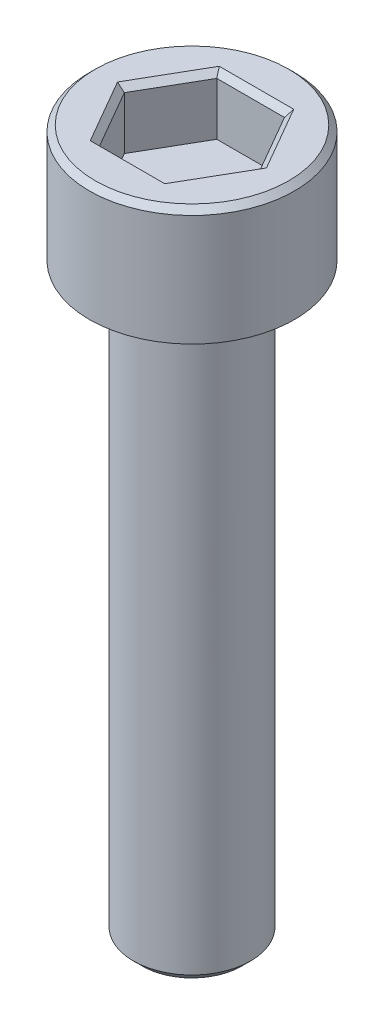
SolidWorks part; units mm, degrees
ref_plane "前视基准面" through (0, 0, 0) normal (0, 0, 1) x (1, 0, 0)
ref_plane "上视基准面" through (0, 0, 0) normal (0, 1, 0) x (1, 0, 0)
ref_plane "右视基准面" through (0, 0, 0) normal (1, 0, 0) x (0, 0, -1)
sketch "草图1" plane through (0, 0, 0) normal (0, 1, 0) x (1, 0, 0)
  circle A0 centre (0, 0) radius 3.5
  dimension "D1" = 7
extrude "凸台-拉伸1" add sketch "草图1" along normal blind 4
sketch "草图2" plane through (0, 0, 0) normal (0, -1, 0) x (1, 0, 0)
  circle A0 centre (0, 0) radius 2
  dimension "D1" = 4
extrude "凸台-拉伸2" add sketch "草图2" along normal blind 20
sketch "草图11" plane through (0, 4, 0) normal (0, 1, 0) x (1, 0, 0)
  line L1 (1.155, 1.9999) -> (-1.1544, 2.0001)
  line L2 (-1.1544, 2.0001) -> (-2.3094, 0.0003)
  line L3 (-2.3094, 0.0003) -> (-1.155, -1.9999)
  line L4 (-1.155, -1.9999) -> (1.1544, -2.0001)
  line L5 (1.1544, -2.0001) -> (2.3094, -0.0003)
  line L6 (2.3094, -0.0003) -> (1.155, 1.9999)
  circle A0 centre (0, 0) radius 2 construction
  dimension "D1" = 4
extrude "切除-拉伸1" cut sketch "草图11" against normal blind 2
chamfer "倒角1" distance 0.2 angle 45 7 edges at (0, 4, 3.5) (0.0003, 4, -2) (-1.7319, 4, -1.0002) (-1.7322, 4, 0.9998) (-0.0003, 4, 2) (1.7319, 4, 1.0002) (1.7322, 4, -0.9998)
chamfer "倒角2" distance 0.3 angle 45 1 edges at (0, -20, -2)
